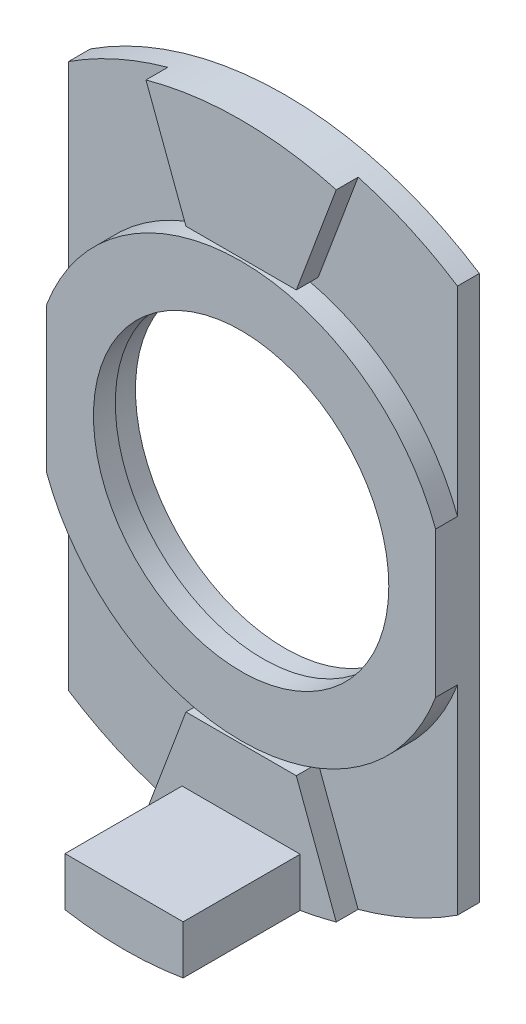
SolidWorks part; units mm, degrees
ref_plane "Front Plane" through (0, 0, 0) normal (0, 0, 1) x (1, 0, 0)
ref_plane "Top Plane" through (0, 0, 0) normal (0, 1, 0) x (1, 0, 0)
ref_plane "Right Plane" through (0, 0, 0) normal (1, 0, 0) x (0, 0, -1)
sketch "Sketch1" plane through (0, 0, 0) normal (0, 0, 1) x (1, 0, 0)
  line L0 (0, 0) -> (6.3542, 0) construction
  line L2 (-4.516, 6.3257) -> (-4.516, -6.3257)
  line L4 (4.516, 6.3257) -> (4.516, -6.3257)
  line L5 (-4.516, 6.3257) -> (4.516, -6.3257) construction
  line L6 (-4.516, -6.3257) -> (4.516, 6.3257) construction
  arc A0 (4.516, -6.3257) -> (-4.516, -6.3257) centre (0, 0.6361) cw
  arc A1 (4.516, 6.3257) -> (-4.516, 6.3257) centre (0, -0.6361) ccw
  circle A3 centre (0, 0) radius 3.47
  point P0 (0, 0)
extrude "Boss-Extrude1" add sketch "Sketch1" along normal blind 0.508
sketch "Sketch2" plane through (0, 0, 0.508) normal (0, 0, 1) x (1, 0, 0)
  line L0 (2.2095, -7.3626) -> (1.2814, -4.884)
  line L1 (1.2814, -4.884) -> (-1.2814, -4.884)
  line L2 (0, 0) -> (0, -12.2914) construction
  line L3 (-2.2095, -7.3626) -> (-1.2814, -4.884)
  arc A0 (-4.516, -6.3257) -> (4.516, -6.3257) centre (0, 0.6361) ccw construction
  arc A1 (2.2095, -7.3626) -> (-2.2095, -7.3626) centre (0, 0.6361) cw
extrude "Boss-Extrude2" add sketch "Sketch2" along normal blind 0.508
sketch "Sketch3" plane through (0, 0, 1.016) normal (0, 0, 1) x (1, 0, 0)
  line L0 (-1.3716, -7.548) -> (-1.3716, -6.4177)
  line L1 (-1.3716, -6.4177) -> (1.3716, -6.4177)
  line L2 (1.3716, -6.4177) -> (1.3716, -7.548)
  line L3 (0, 0) -> (0, -8.2871) construction
  arc A0 (-1.3716, -7.548) -> (1.3716, -7.548) centre (0, 0.6361) ccw
  arc A1 (-2.2095, -7.3626) -> (2.2095, -7.3626) centre (0, 0.6361) ccw construction
  dimension "D1" = 0.8379
  dimension "D2" = 1.1303
  dimension "D3" = 2.7432
extrude "Boss-Extrude3" add sketch "Sketch3" along normal blind 2.7178
sketch "Sketch4" plane through (0, 0, 0.508) normal (0, 0, 1) x (1, 0, 0)
  line L0 (4.516, -6.3257) -> (4.516, 6.3257) construction
  line L1 (4.516, -1.6927) -> (4.516, 1.6927)
  line L2 (-4.516, 6.3257) -> (-4.516, -6.3257) construction
  line L3 (-4.516, 1.6927) -> (-4.516, -1.6927)
  circle A0 centre (0, 0) radius 3.429
  arc A1 (4.516, 1.6927) -> (-4.516, 1.6927) centre (0, 0) ccw
  arc A2 (-4.516, -1.6927) -> (4.516, -1.6927) centre (0, 0) ccw
extrude "Boss-Extrude4" add sketch "Sketch4" along normal blind 0.508
mirror "Mirror1" about plane through (0, 0, 0) normal (0, 1, 0) of "Boss-Extrude2"
